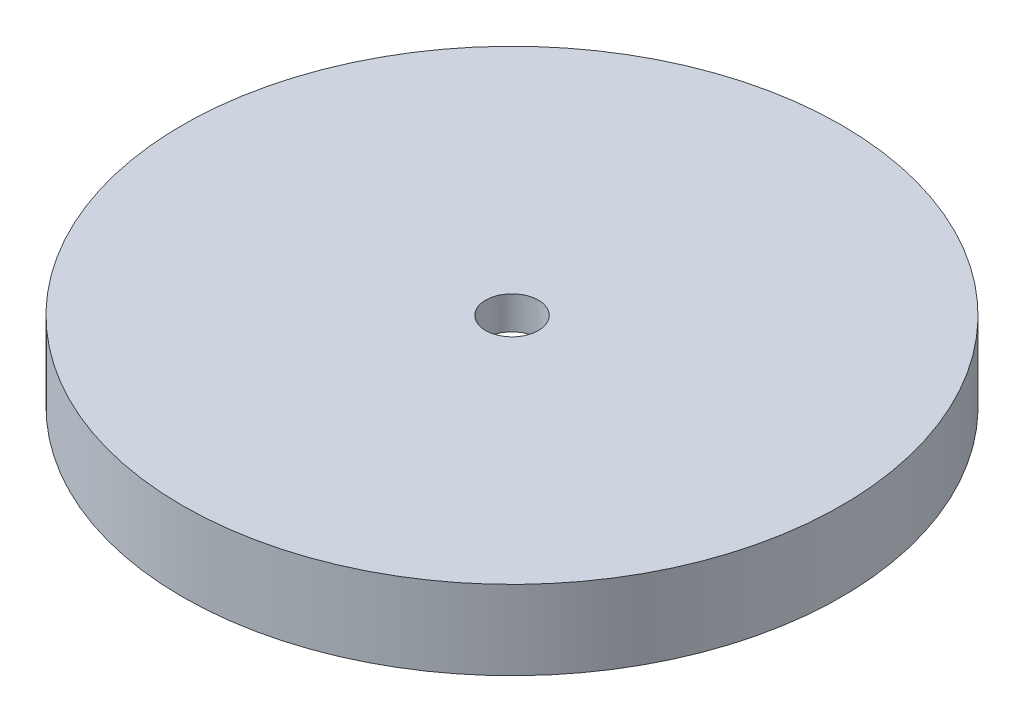
SolidWorks part; units mm, degrees
ref_plane "Front Plane" through (0, 0, 0) normal (0, 0, 1) x (1, 0, 0)
ref_plane "Top Plane" through (0, 0, 0) normal (0, 1, 0) x (1, 0, 0)
ref_plane "Right Plane" through (0, 0, 0) normal (1, 0, 0) x (0, 0, -1)
sketch "Sketch1" plane through (0, 0, 0) normal (0, 1, 0) x (1, 0, 0)
  circle A0 centre (0, 0) radius 40
  circle A1 centre (0, 0) radius 50
  dimension "D1" = 80
  dimension "D2" = 10
extrude "Boss-Extrude1" add sketch "Sketch1" along normal blind 7
sketch "Sketch2" plane through (0, 7, 0) normal (0, 1, 0) x (1, 0, 0)
  circle A0 centre (0, 0) radius 4
  circle A1 centre (0, 0) radius 50
  circle A2 centre (0, 0) radius 50
  dimension "D2" = 8
  dimension "D1" = 0
extrude "Boss-Extrude2" add sketch "Sketch2" along normal blind 5
